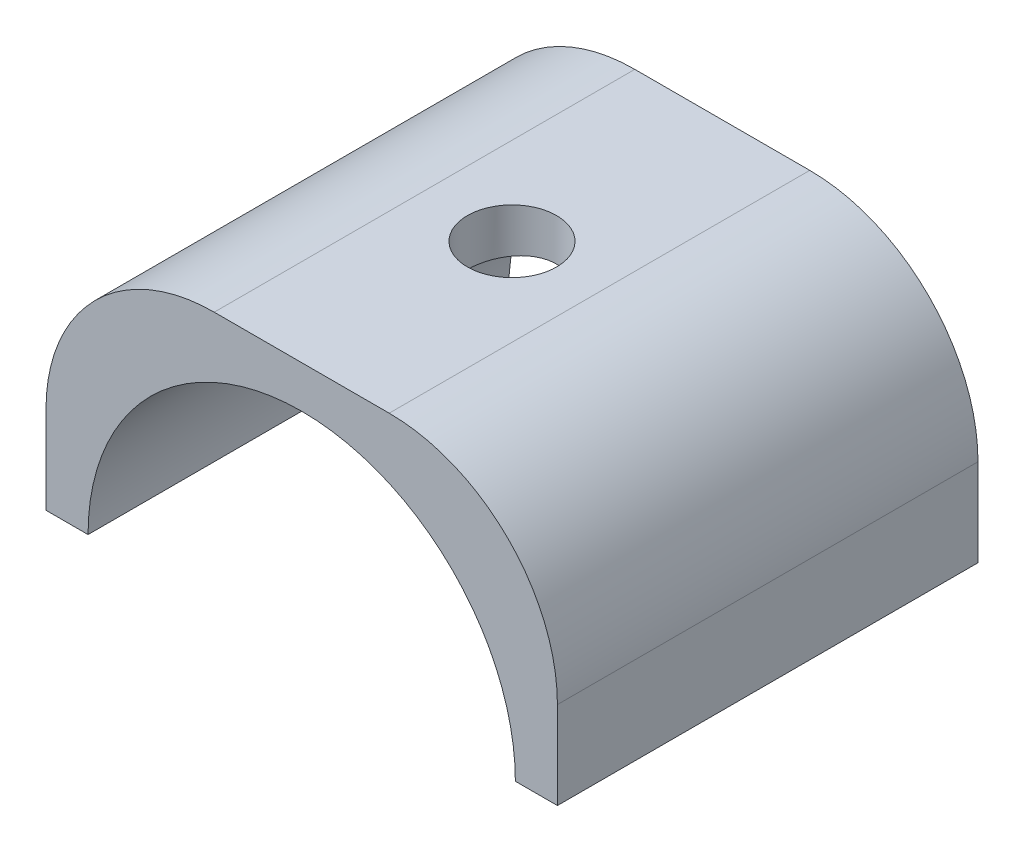
SolidWorks part; units mm, degrees
material "1060 Alloy"
ref_plane "Front Plane" through (0, 0, 0) normal (0, 0, 1) x (1, 0, 0)
ref_plane "Top Plane" through (0, 0, 0) normal (0, 1, 0) x (1, 0, 0)
ref_plane "Right Plane" through (0, 0, 0) normal (1, 0, 0) x (0, 0, -1)
sketch "Sketch1" plane through (0, 0, 0) normal (0, 0, 1) x (1, 0, 0)
  line L0 (-15.2, 0) -> (-12.7, 0)
  line L2 (15.2, 0) -> (15.2, 5.2)
  line L3 (5.2, 15.2) -> (-5.2, 15.2)
  line L4 (-15.2, 0) -> (-15.2, 5.2)
  line L5 (15.2, -15.2) -> (-15.2, 15.2) construction
  line L6 (15.2, 15.2) -> (-15.2, -15.2) construction
  line L7 (12.7, 0) -> (15.2, 0)
  line L8 (-12.7, 0) -> (0, 0) construction
  line L9 (0, 0) -> (12.7, 0) construction
  arc A0 (12.7, 0) -> (-12.7, 0) centre (0, 0) ccw
  arc A2 (15.2, 5.2) -> (5.2, 15.2) centre (5.2, 5.2) ccw
  arc A5 (-5.2, 15.2) -> (-15.2, 5.2) centre (-5.2, 5.2) ccw
  point P1 (0, 15.2)
  dimension "D1" = 25.4
  dimension "D2" = 10
  dimension "D4" = 30.4
  dimension "D3" = 15.2
extrude "Boss-Extrude1" add sketch "Sketch1" along normal mid plane 25
hole_wizard "M5 Clearance Hole1" positions "Sketch2" profile "Sketch3" hole size "M5" standard "ANSI Metric" end condition through all
sketch "Sketch2" plane through (0, 15.2, 0) normal (0, 1, 0) x (1, 0, 0)
  point P0 (0, 0)
sketch "Sketch3" plane through (0, 15.2, 0) normal (1, 0, 0) x (0, 0, 1)
  line L0 (0, 0) -> (0, 15.2)
  line L1 (0, 15.2) -> (2.65, 15.2)
  line L2 (2.65, 15.2) -> (2.65, 0)
  line L5 (2.65, 0) -> (0, 0)
  line L11 (0, -6.35) -> (0, 107.95) construction
  dimension "Thru Hole Dia." = 5.3
  dimension "Thru Hole Depth" = 15.2
sketch "Sketch4" plane through (0, 0, 0) normal (0, -1, 0) x (1, 0, 0)
  line L0 (-13.95, 0) -> (-15.2, 0) construction
  line L1 (-14.45, -10) -> (-13.45, -10)
  line L2 (-14.45, -10) -> (-14.45, 10)
  line L3 (-14.45, 10) -> (-13.45, 10)
  line L4 (-13.45, -10) -> (-13.45, 10)
  line L5 (-14.45, -10) -> (-13.45, 10) construction
  line L6 (-14.45, 10) -> (-13.45, -10) construction
  line L7 (-15.2, 12.5) -> (-15.2, -12.5) construction
  line L8 (-13.95, 0) -> (-12.7, 0) construction
  line L9 (-12.7, 12.5) -> (-12.7, -12.5) construction
  line L10 (0, 10.8415) -> (0, -9.0344) construction
  line L11 (14.45, -10) -> (13.45, -10)
  line L12 (14.45, -10) -> (14.45, 10)
  line L13 (14.45, 10) -> (13.45, 10)
  line L14 (13.45, -10) -> (13.45, 10)
  point P0 (-13.95, 0)
  dimension "D1" = 20
  dimension "D2" = 1
extrude "Cut-Extrude1" cut sketch "Sketch4" against normal blind 3
equation "\"keelOutDiameter\"= 1in"
equation "\"keelInDiameter\"= \"keelOutDiameter\" - 0.125in"
equation "\"frontBoltClearance\"= 7.25mm"
equation "\"betweenBoltsDistance\"= 20mm"
equation "\"wingLength\"= 1.4m"
equation "\"frontTubeLength\"= \"wingLength\" / sin ( 34.95deg )"
equation "\"plateThickness\"= 5mm"
equation "\"crossBarOutDiameter\"= 1in"
equation "\"crossBarInDiameter\"= \"crossBarOutDiameter\" - 0.125in"
equation "\"frontToCrossBar\"= 466mm"
equation "\"D1@Sketch1\"=\"keelOutDiameter\""
equation "\"D4@Sketch1\"=\"keelOutDiameter\"+5mm"
equation "\"D3@Sketch1\"=\"keelOutDiameter\"/2+2.5"
